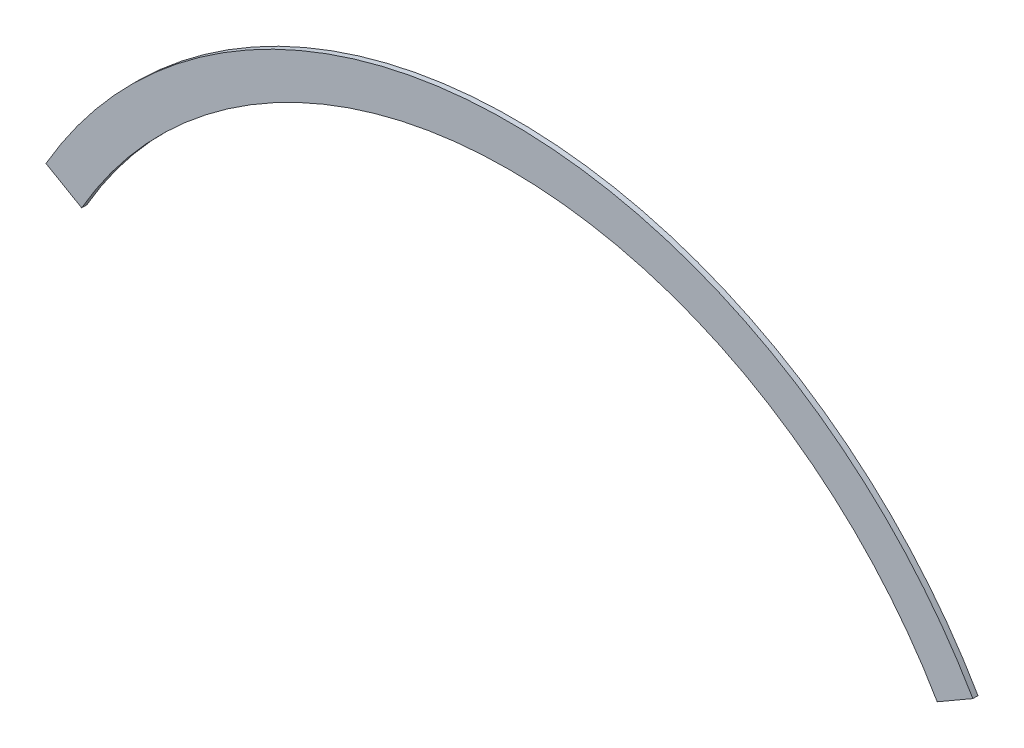
SolidWorks part; units mm, degrees
material "PE High Density"
ref_plane "Front Plane" through (0, 0, 0) normal (0, 0, 1) x (1, 0, 0)
ref_plane "Top Plane" through (0, 0, 0) normal (0, 1, 0) x (1, 0, 0)
ref_plane "Right Plane" through (0, 0, 0) normal (1, 0, 0) x (0, 0, -1)
sketch "Sketch1" plane through (0, 0, 0) normal (0, 0, 1) x (1, 0, 0)
  line L0 (-142.9808, 82.55) -> (-131.9823, 76.2)
  line L1 (131.9823, 76.2) -> (142.9808, 82.55)
  arc A0 (-142.9808, 82.55) -> (142.9808, 82.55) centre (0, 0) cw
  arc A1 (-131.9823, 76.2) -> (131.9823, 76.2) centre (0, 0) cw
  point P6 (0, 152.4)
  dimension "D1" = 152.4
  dimension "D2" = 12.7
  dimension "D3" = 120
extrude "Boss-Extrude1" add sketch "Sketch1" along normal blind 1.5875
